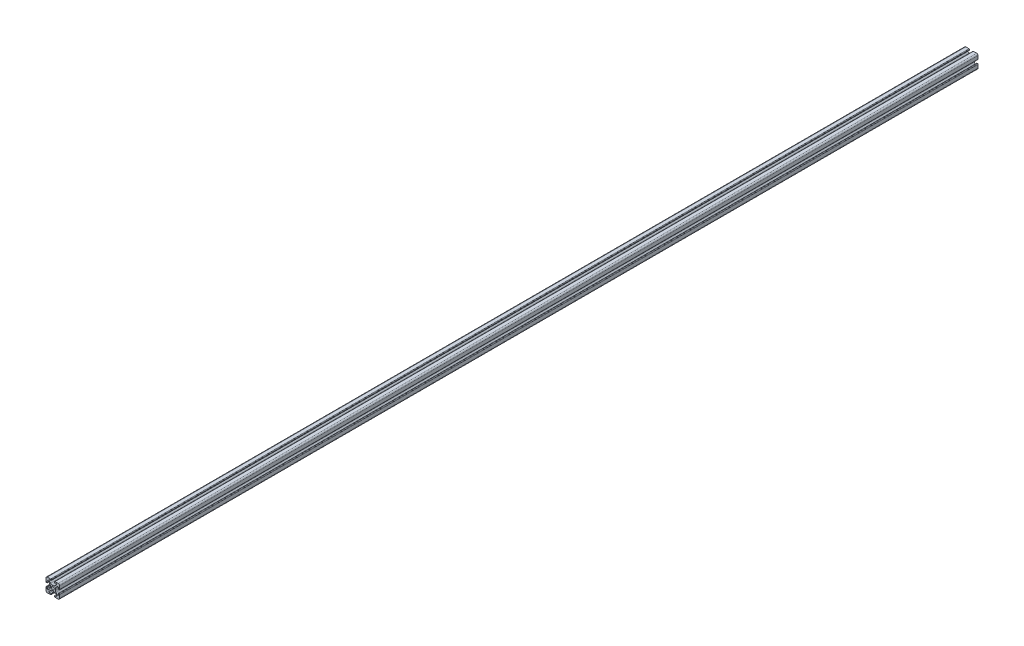
SolidWorks part; units mm, degrees
ref_plane "Front Plane" through (0, 0, 0) normal (0, 0, 1) x (1, 0, 0)
ref_plane "Top Plane" through (0, 0, 0) normal (0, 1, 0) x (1, 0, 0)
ref_plane "Right Plane" through (0, 0, 0) normal (1, 0, 0) x (0, 0, -1)
sketch "Sketch1" plane through (0, 0, 0) normal (0, 0, 1) x (1, 0, 0)
  line L0 (0, 10) -> (0, -10) construction
  line L1 (10, 0) -> (-10, 0) construction
  line L2 (-2.5, 10) -> (2.5, 10) construction
  line L3 (-5.75, 8.2) -> (5.75, 8.2) construction
  circle A0 centre (0, 0) radius 2.15 construction
  point P4 (0, 0)
  point P8 (0, 0)
  point P10 (0, 3.6)
  point P14 (0, 10)
  point P17 (0, 8.2)
  dimension "Thru Hole" = 4.3
  dimension "Height" = 20
  dimension "T Slot Depth" = 6.4
  dimension "T Slot Top Width" = 5
  dimension "T Slot Max Width" = 11.5
  dimension "Wall" = 1.8
sketch "Sketch2" plane through (0, 0, 0) normal (1, 0, 0) x (0, 0, -1)
  line L0 (675, 0) -> (-675, 0) construction
  point P4 (0, 0)
  dimension "D1" = 1350
sketch "Sketch3" plane through (0, 0, 0) normal (0, 0, 1) x (1, 0, 0)
  line L0 (3.2874, 10) -> (8, 10)
  line L1 (10, 8) -> (10, -8) construction
  line L2 (8, -10) -> (-8, -10) construction
  line L3 (-10, 10) -> (10, -10) construction
  line L4 (2.5, 9.2126) -> (2.5, 8.5048)
  line L5 (-5.75, 8.2) -> (5.75, 8.2) construction
  line L6 (2.8048, 8.2) -> (4.9118, 8.2)
  line L7 (5.5045, 6.7691) -> (3.2141, 4.4787)
  line L8 (1.0928, 3.6) -> (-1.0928, 3.6)
  line L9 (0, 10) -> (0, -10) construction
  line L10 (5.75, 8.2) -> (5.75, 0) construction
  line L11 (10, 0) -> (-10, 0) construction
  line L12 (0, 0) -> (0, 10) construction
  line L13 (-2.5, 9.2126) -> (-2.5, 8.5048)
  line L14 (-5.5045, 6.7691) -> (-3.2141, 4.4787)
  line L15 (-2.8048, 8.2) -> (-4.9118, 8.2)
  line L16 (-3.2874, 10) -> (-8, 10)
  line L17 (0, 0) -> (-10, 0) construction
  line L18 (-10, 3.2874) -> (-10, 8)
  line L19 (-8.2, 2.8048) -> (-8.2, 4.9118)
  line L20 (-6.7691, 5.5045) -> (-4.4787, 3.2141)
  line L21 (-9.2126, 2.5) -> (-8.5048, 2.5)
  line L22 (-3.6, -1.0928) -> (-3.6, 1.0928)
  line L23 (-6.7691, -5.5045) -> (-4.4787, -3.2141)
  line L24 (-8.2, -2.8048) -> (-8.2, -4.9118)
  line L25 (-9.2126, -2.5) -> (-8.5048, -2.5)
  line L26 (-10, -3.2874) -> (-10, -8)
  line L27 (9.2126, -2.5) -> (8.5048, -2.5)
  line L28 (8.2, -2.8048) -> (8.2, -4.9118)
  line L29 (6.7691, -5.5045) -> (4.4787, -3.2141)
  line L30 (3.6, -1.0928) -> (3.6, 1.0928)
  line L31 (9.2126, 2.5) -> (8.5048, 2.5)
  line L32 (6.7691, 5.5045) -> (4.4787, 3.2141)
  line L33 (8.2, 2.8048) -> (8.2, 4.9118)
  line L34 (10, 8) -> (10, 3.2874)
  line L35 (10, -3.2874) -> (10, -8)
  line L36 (3.2874, -10) -> (8, -10)
  line L37 (-3.2874, -10) -> (-8, -10)
  line L38 (-6.7691, -5.5045) -> (-4.4787, -3.2141)
  line L39 (-2.8048, -8.2) -> (-4.9118, -8.2)
  line L40 (-5.5045, -6.7691) -> (-3.2141, -4.4787)
  line L41 (-2.5, -9.2126) -> (-2.5, -8.5048)
  line L42 (1.0928, -3.6) -> (-1.0928, -3.6)
  line L43 (5.5045, -6.7691) -> (3.2141, -4.4787)
  line L44 (2.8048, -8.2) -> (4.9118, -8.2)
  line L45 (2.5, -9.2126) -> (2.5, -8.5048)
  arc A0 (4.9118, 8.2) -> (5.5045, 6.7691) centre (4.9118, 7.3618) cw
  arc A1 (3.2141, 4.4787) -> (1.0928, 3.6) centre (1.0928, 6.6) cw
  circle A2 centre (0, 0) radius 2.15 construction
  circle A3 centre (0, 0) radius 2.15
  arc A4 (3.2874, 10) -> (2.5, 9.2126) centre (3.2874, 9.2126) ccw
  arc A5 (2.5, 8.5048) -> (2.8048, 8.2) centre (2.8048, 8.5048) ccw
  arc A6 (-3.2874, 10) -> (-2.5, 9.2126) centre (-3.2874, 9.2126) cw
  arc A7 (-4.9118, 8.2) -> (-5.5045, 6.7691) centre (-4.9118, 7.3618) ccw
  arc A8 (-3.2141, 4.4787) -> (-1.0928, 3.6) centre (-1.0928, 6.6) ccw
  arc A9 (-2.5, 8.5048) -> (-2.8048, 8.2) centre (-2.8048, 8.5048) cw
  arc A10 (-8.5048, 2.5) -> (-8.2, 2.8048) centre (-8.5048, 2.8048) ccw
  arc A11 (-4.4787, 3.2141) -> (-3.6, 1.0928) centre (-6.6, 1.0928) cw
  arc A12 (-8.2, 4.9118) -> (-6.7691, 5.5045) centre (-7.3618, 4.9118) cw
  arc A13 (-10, 3.2874) -> (-9.2126, 2.5) centre (-9.2126, 3.2874) ccw
  arc A14 (-8.5048, -2.5) -> (-8.2, -2.8048) centre (-8.5048, -2.8048) cw
  arc A15 (-10, -3.2874) -> (-9.2126, -2.5) centre (-9.2126, -3.2874) cw
  arc A16 (-4.4787, -3.2141) -> (-3.6, -1.0928) centre (-6.6, -1.0928) ccw
  arc A17 (-8.2, -4.9118) -> (-6.7691, -5.5045) centre (-7.3618, -4.9118) ccw
  arc A26 (-8, -10) -> (-10, -8) centre (-8, -8) cw
  arc A27 (-8, 10) -> (-10, 8) centre (-8, 8) ccw
  arc A28 (8, 10) -> (10, 8) centre (8, 8) cw
  arc A29 (10, -8) -> (8, -10) centre (8, -8) cw
  arc A30 (8.2, -4.9118) -> (6.7691, -5.5045) centre (7.3618, -4.9118) cw
  arc A31 (4.4787, -3.2141) -> (3.6, -1.0928) centre (6.6, -1.0928) cw
  arc A32 (10, -3.2874) -> (9.2126, -2.5) centre (9.2126, -3.2874) ccw
  arc A33 (8.5048, -2.5) -> (8.2, -2.8048) centre (8.5048, -2.8048) ccw
  arc A34 (10, 3.2874) -> (9.2126, 2.5) centre (9.2126, 3.2874) cw
  arc A35 (8.2, 4.9118) -> (6.7691, 5.5045) centre (7.3618, 4.9118) ccw
  arc A36 (4.4787, 3.2141) -> (3.6, 1.0928) centre (6.6, 1.0928) ccw
  arc A37 (8.5048, 2.5) -> (8.2, 2.8048) centre (8.5048, 2.8048) cw
  arc A38 (-2.5, -8.5048) -> (-2.8048, -8.2) centre (-2.8048, -8.5048) ccw
  arc A39 (-3.2141, -4.4787) -> (-1.0928, -3.6) centre (-1.0928, -6.6) cw
  arc A40 (-4.9118, -8.2) -> (-5.5045, -6.7691) centre (-4.9118, -7.3618) cw
  arc A41 (-3.2874, -10) -> (-2.5, -9.2126) centre (-3.2874, -9.2126) ccw
  arc A42 (2.5, -8.5048) -> (2.8048, -8.2) centre (2.8048, -8.5048) cw
  arc A43 (3.2874, -10) -> (2.5, -9.2126) centre (3.2874, -9.2126) cw
  arc A44 (3.2141, -4.4787) -> (1.0928, -3.6) centre (1.0928, -6.6) ccw
  arc A45 (4.9118, -8.2) -> (5.5045, -6.7691) centre (4.9118, -7.3618) ccw
  point P36 (2.5, 10)
  point P39 (2.5, 8.2)
  point P49 (0, 3.6)
  point P77 (-3.6, 0)
  point P78 (-8.2, -2.5)
  point P79 (-10, -2.5)
  point P104 (-10, -10)
  point P110 (10, 10)
  point P114 (10, -2.5)
  point P115 (8.2, -2.5)
  point P116 (3.6, 0)
  point P141 (0, -3.6)
  dimension "D1" = 3
  dimension "D2" = 0.8382
  dimension "D4" = 0.7874
  dimension "D5" = 0.3048
  dimension "D6" = 2
  dimension "D3" = 45
extrude "Boss-Extrude1" add sketch "Sketch3" along normal up to vertex (675 mm away) and the other way up to vertex (675 mm away) contours A45 L44 A42 L45 A43 L36 A29 L35 A32 L27 A33 L28 A30 L29 A31 L30 A36 L32 A35 L33 A37 L31 A34 L34 A28 L0 A4 L4 A5 L6 A0 L7 A1 L8 A8 L14 A7 L15 A9 L13 A6 L16 A27 L18 A13 L21 A10 L19 A12 L20 A11 up to point (0, 0, 675) other way up to point (0, 0, -675)
